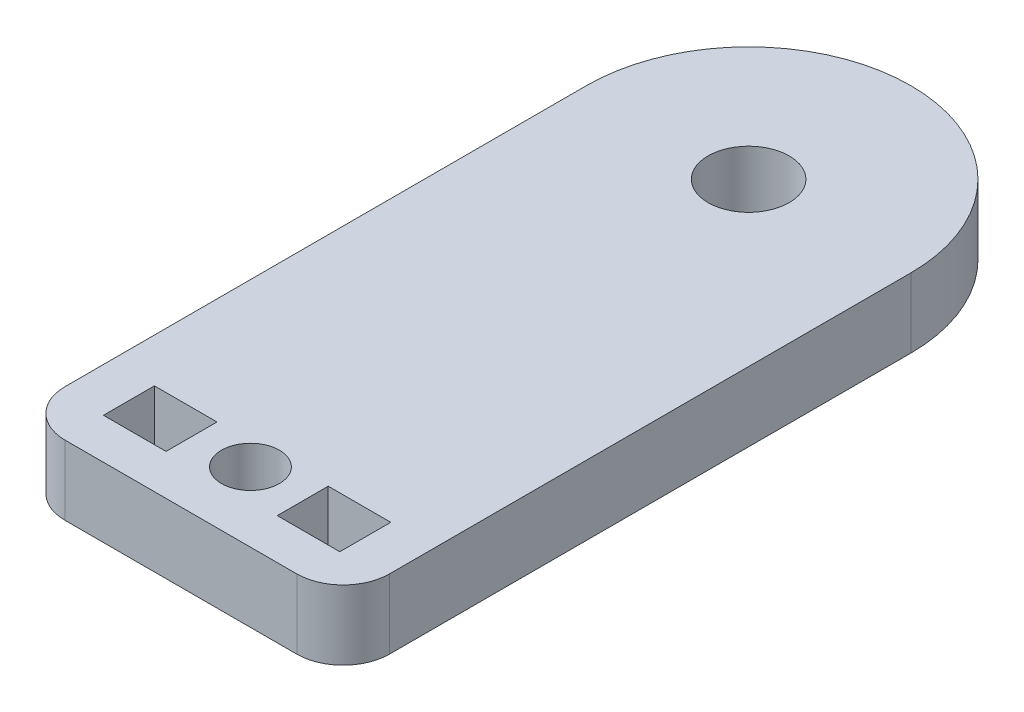
SolidWorks part; units mm, degrees
ref_plane "前视基准面" through (0, 0, 0) normal (0, 0, 1) x (1, 0, 0)
ref_plane "上视基准面" through (0, 0, 0) normal (0, 1, 0) x (1, 0, 0)
ref_plane "右视基准面" through (0, 0, 0) normal (1, 0, 0) x (0, 0, -1)
sketch "草图1" plane through (0, 0, 0) normal (0, 1, 0) x (1, 0, 0)
  line L0 (0, 0) -> (0, -12.25) construction
  line L1 (-5, -12.25) -> (5, -12.25)
  line L2 (-7, -10.25) -> (-7, 12.25)
  line L3 (-7, 12.25) -> (7, 12.25)
  line L4 (7, -10.25) -> (7, 12.25)
  line L5 (-7, -12.25) -> (7, 12.25) construction
  line L6 (-7, 12.25) -> (7, -12.25) construction
  line L7 (-5.1, -10.4934) -> (-2.4, -10.4934)
  line L8 (-5.1, -10.4934) -> (-5.1, -8.2934)
  line L9 (-5.1, -8.2934) -> (-2.4, -8.2934)
  line L10 (-2.4, -10.4934) -> (-2.4, -8.2934)
  line L11 (-5.1, -10.4934) -> (-2.4, -8.2934) construction
  line L12 (-5.1, -8.2934) -> (-2.4, -10.4934) construction
  line L13 (5.1, -10.4934) -> (2.4, -10.4934)
  line L14 (5.1, -10.4934) -> (5.1, -8.2934)
  line L15 (5.1, -8.2934) -> (2.4, -8.2934)
  line L16 (2.4, -10.4934) -> (2.4, -8.2934)
  circle A0 centre (0, 12.25) radius 7
  circle A1 centre (0, 12.25) radius 1.75
  circle A2 centre (0, -9.25) radius 1.25
  arc A3 (5, -12.25) -> (7, -10.25) centre (5, -10.25) ccw
  arc A4 (-5, -12.25) -> (-7, -10.25) centre (-5, -10.25) cw
  point P0 (0, 0)
  point P17 (-3.75, -9.3934)
  dimension "D1" = 14
  dimension "D3" = 3.5
  dimension "D4" = 2.5
  dimension "D6" = 2
  dimension "D2" = 24.5
  dimension "D5" = 3
  dimension "D7" = 2.7
  dimension "D8" = 2.2
  dimension "D9" = 7
  dimension "D10" = 3.75
extrude "凸台-拉伸1" add sketch "草图1" along normal blind 3 contours A4 L1 A3 L4 A0 L2 A2 | A1 L3 A0 | A1 L3 A0
